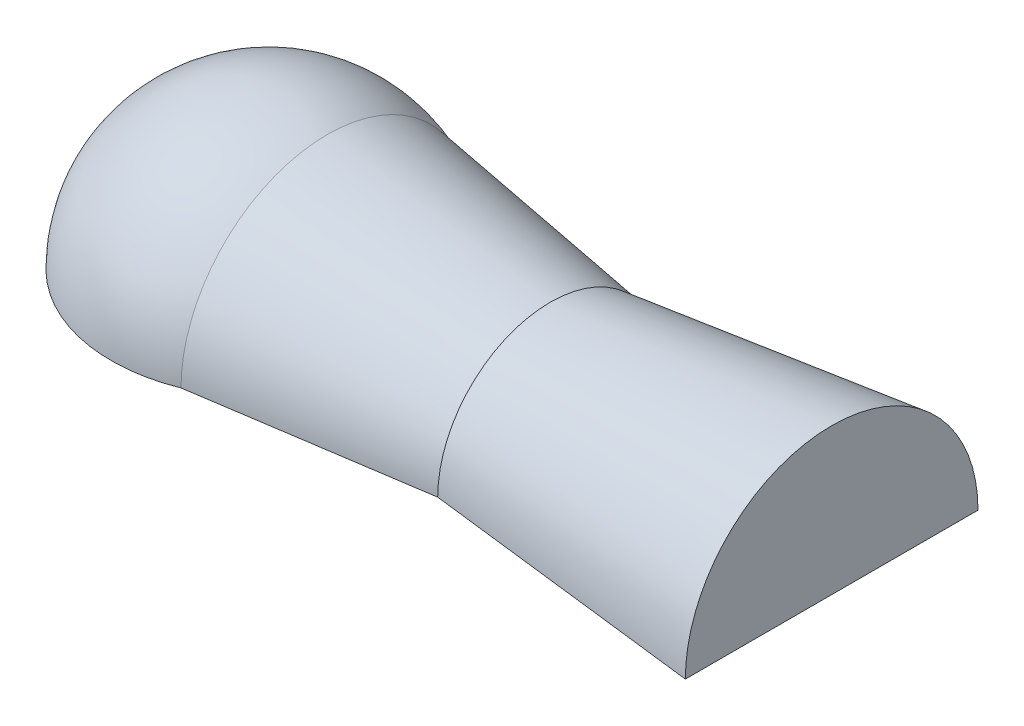
SolidWorks part; units mm, degrees
ref_plane "Спереди" through (0, 0, 0) normal (0, 0, 1) x (1, 0, 0)
ref_plane "Сверху" through (0, 0, 0) normal (0, 1, 0) x (1, 0, 0)
ref_plane "Справа" through (0, 0, 0) normal (1, 0, 0) x (0, 0, -1)
sketch "Эскиз1" plane through (0, 0, 0) normal (0, 1, 0) x (1, 0, 0)
  line L0 (0, 0) -> (250, 0)
  line L1 (25.9808, 65) -> (125, 50)
  line L2 (125, 50) -> (250, 65)
  line L3 (0, 0) -> (-70, 0)
  line L4 (250, 65) -> (250, 0)
  arc A0 (25.9808, 65) -> (-70, 0) centre (0, 0) ccw
  point P0 (0, 0)
  point P5 (70, 0)
  dimension "D2" = 140
  dimension "D1" = 250
  dimension "D3" = 50
  dimension "D4" = 65
  dimension "D5" = 125
  dimension "D6" = 65
revolve "Повернуть1" add sketch "Эскиз1" angle 180 about L0
